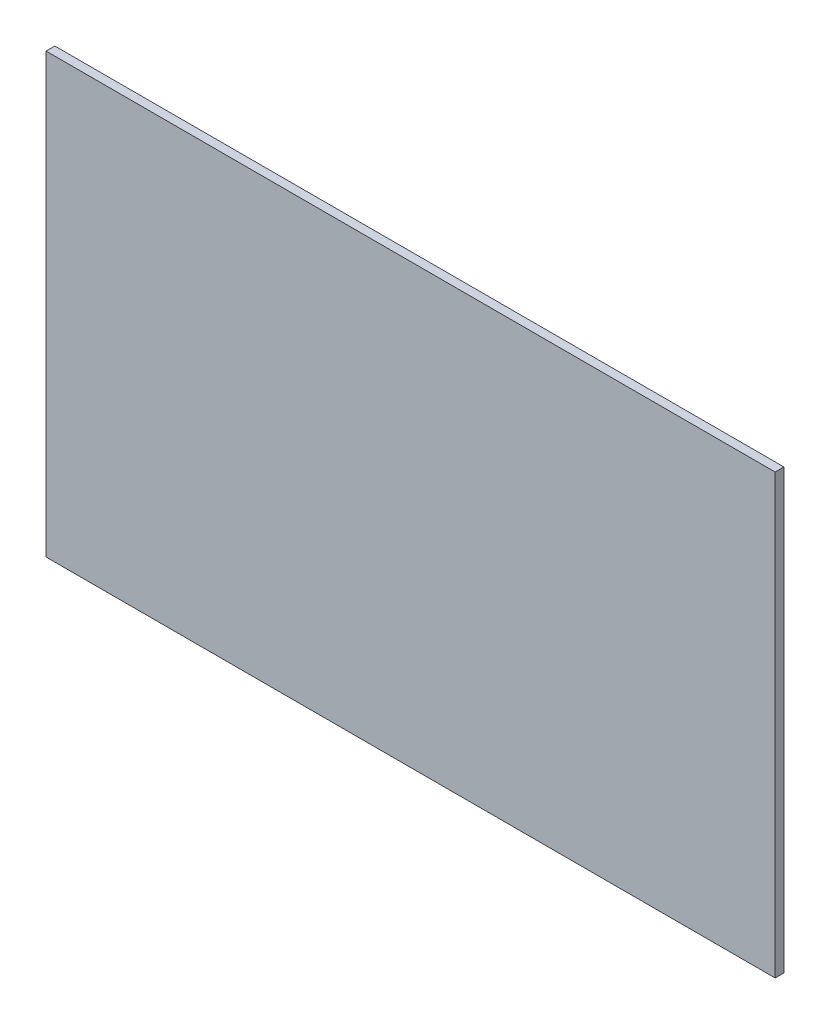
SolidWorks part; units mm, degrees
ref_plane "Front Plane" through (0, 0, 0) normal (0, 0, 1) x (1, 0, 0)
ref_plane "Top Plane" through (0, 0, 0) normal (0, 1, 0) x (1, 0, 0)
ref_plane "Right Plane" through (0, 0, 0) normal (1, 0, 0) x (0, 0, -1)
sketch "Sketch1" plane through (0, 0, 0) normal (0, 0, 1) x (1, 0, 0)
  line L1 (0, 0) -> (249.6, 0)
  line L2 (0, 0) -> (0, -150)
  line L3 (0, -150) -> (249.6, -150)
  line L4 (249.6, 0) -> (249.6, -150)
  dimension "D1" = 150
  dimension "D2" = 249.6
extrude "Boss-Extrude1" add sketch "Sketch1" along normal blind 3
